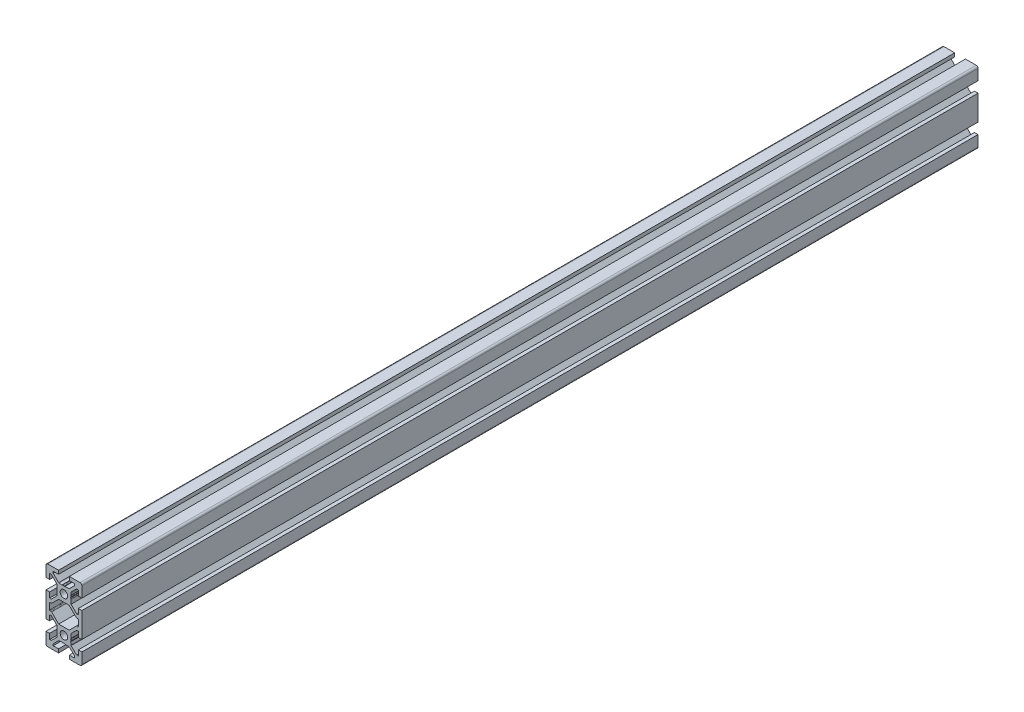
SolidWorks part; units mm, degrees
ref_plane "Front Plane" through (0, 0, 0) normal (0, 0, 1) x (1, 0, 0)
ref_plane "Top Plane" through (0, 0, 0) normal (0, 1, 0) x (1, 0, 0)
ref_plane "Right Plane" through (0, 0, 0) normal (1, 0, 0) x (0, 0, -1)
ref_plane "Plane1" through (0, 0, -600) normal (0, 0, -1) x (-1, 0, 0)
sketch "Sketch1" plane through (0, 0, -600) normal (0, 0, -1) x (-1, 0, 0)
  line L0 (8, 1.7) -> (8, -1.7)
  line L1 (7.7, -2) -> (7.0636, -2)
  line L2 (6.8515, -2.0879) -> (2.9393, -6)
  line L3 (2.9393, -6) -> (-2.9393, -6)
  line L4 (-2.9393, -6) -> (-6.8515, -2.0879)
  line L5 (-7.0636, -2) -> (-7.7, -2)
  line L6 (-8, -1.7) -> (-8, 1.7)
  line L7 (-7.7, 2) -> (-7.0636, 2)
  line L8 (-6.8515, 2.0879) -> (-2.9393, 6)
  line L9 (-2.9393, 6) -> (2.9393, 6)
  line L10 (2.9393, 6) -> (6.8515, 2.0879)
  line L11 (7.0636, 2) -> (7.7, 2)
  line L12 (10, -7) -> (10, 7)
  line L13 (10, 7) -> (8, 7)
  line L14 (8, 7) -> (8, 4)
  line L15 (8, 4) -> (7.0607, 4)
  line L16 (7.0607, 4) -> (4, 7.0607)
  line L17 (4, 7.0607) -> (4, 7.5)
  line L18 (4, 7.5) -> (3.751, 8.7811)
  line L19 (3.751, 8.7811) -> (3.933, 9.0964)
  line L20 (3.933, 9.5964) -> (3.7, 10)
  line L21 (3.7, 10) -> (3.933, 10.4036)
  line L22 (4, 10.6536) -> (4, 12.9393)
  line L23 (4, 12.9393) -> (7.0607, 16)
  line L24 (7.0607, 16) -> (8, 16)
  line L25 (8, 16) -> (8, 13)
  line L26 (8, 13) -> (10, 13)
  line L27 (10, 13) -> (10, 19)
  line L28 (9, 20) -> (3, 20)
  line L29 (3, 20) -> (3, 18)
  line L30 (3, 18) -> (6, 18)
  line L31 (6, 18) -> (6, 17.0607)
  line L32 (6, 17.0607) -> (2.9393, 14)
  line L33 (2.9393, 14) -> (2.5, 14)
  line L34 (2.5, 14) -> (1.2189, 13.751)
  line L35 (1.2189, 13.751) -> (0.9036, 13.933)
  line L36 (0.4036, 13.933) -> (0, 13.7)
  line L37 (0, 13.7) -> (-0.4036, 13.933)
  line L38 (-0.6536, 14) -> (-2.9393, 14)
  line L39 (-2.9393, 14) -> (-6, 17.0607)
  line L40 (-6, 17.0607) -> (-6, 18)
  line L41 (-6, 18) -> (-3, 18)
  line L42 (-3, 18) -> (-3, 20)
  line L43 (-3, 20) -> (-9, 20)
  line L44 (-10, 19) -> (-10, 13)
  line L45 (-10, 13) -> (-8, 13)
  line L46 (-8, 13) -> (-8, 16)
  line L47 (-8, 16) -> (-7.0607, 16)
  line L48 (-7.0607, 16) -> (-4, 12.9393)
  line L49 (-4, 12.9393) -> (-4, 12.5)
  line L50 (-4, 12.5) -> (-3.751, 11.2189)
  line L51 (-3.751, 11.2189) -> (-3.933, 10.9036)
  line L52 (-3.933, 10.4036) -> (-3.7, 10)
  line L53 (-3.7, 10) -> (-3.933, 9.5964)
  line L54 (-4, 9.3464) -> (-4, 7.0607)
  line L55 (-4, 7.0607) -> (-7.0607, 4)
  line L56 (-7.0607, 4) -> (-8, 4)
  line L57 (-8, 4) -> (-8, 7)
  line L58 (-8, 7) -> (-10, 7)
  line L59 (-10, 7) -> (-10, -7)
  line L60 (-10, -7) -> (-8, -7)
  line L61 (-8, -7) -> (-8, -4)
  line L62 (-8, -4) -> (-7.0607, -4)
  line L63 (-7.0607, -4) -> (-4, -7.0607)
  line L64 (-4, -7.0607) -> (-4, -9.3464)
  line L65 (-3.933, -9.5964) -> (-3.7, -10)
  line L66 (-3.7, -10) -> (-3.933, -10.4036)
  line L67 (-3.933, -10.9036) -> (-3.751, -11.2189)
  line L68 (-3.751, -11.2189) -> (-4, -12.5)
  line L69 (-4, -12.5) -> (-4, -12.9393)
  line L70 (-4, -12.9393) -> (-7.0607, -16)
  line L71 (-7.0607, -16) -> (-8, -16)
  line L72 (-8, -16) -> (-8, -13)
  line L73 (-8, -13) -> (-10, -13)
  line L74 (-10, -13) -> (-10, -19)
  line L75 (-9, -20) -> (-3, -20)
  line L76 (-3, -20) -> (-3, -18)
  line L77 (-3, -18) -> (-6, -18)
  line L78 (-6, -18) -> (-6, -17.0607)
  line L79 (-6, -17.0607) -> (-2.9393, -14)
  line L80 (-2.9393, -14) -> (-0.6536, -14)
  line L81 (-0.4036, -13.933) -> (0, -13.7)
  line L82 (0, -13.7) -> (0.4036, -13.933)
  line L83 (0.9036, -13.933) -> (1.2189, -13.751)
  line L84 (1.2189, -13.751) -> (2.5, -14)
  line L85 (2.5, -14) -> (2.9393, -14)
  line L86 (2.9393, -14) -> (6, -17.0607)
  line L87 (6, -17.0607) -> (6, -18)
  line L88 (6, -18) -> (3, -18)
  line L89 (3, -18) -> (3, -20)
  line L90 (3, -20) -> (9, -20)
  line L91 (10, -19) -> (10, -13)
  line L92 (10, -13) -> (8, -13)
  line L93 (8, -13) -> (8, -16)
  line L94 (8, -16) -> (7.0607, -16)
  line L95 (7.0607, -16) -> (4, -12.9393)
  line L96 (4, -12.9393) -> (4, -10.6536)
  line L97 (3.933, -10.4036) -> (3.7, -10)
  line L98 (3.7, -10) -> (3.933, -9.5964)
  line L99 (3.933, -9.0964) -> (3.751, -8.7811)
  line L100 (3.751, -8.7811) -> (4, -7.5)
  line L101 (4, -7.5) -> (4, -7.0607)
  line L102 (4, -7.0607) -> (7.0607, -4)
  line L103 (7.0607, -4) -> (8, -4)
  line L104 (8, -4) -> (8, -7)
  line L105 (8, -7) -> (10, -7)
  circle A0 centre (0, -10) radius 2.1
  circle A1 centre (0, 10) radius 2.1
  arc A2 (7.7, 2) -> (8, 1.7) centre (7.7, 1.7) cw
  arc A3 (8, -1.7) -> (7.7, -2) centre (7.7, -1.7) cw
  arc A4 (7.0636, -2) -> (6.8515, -2.0879) centre (7.0636, -2.3) ccw
  arc A5 (-6.8515, -2.0879) -> (-7.0636, -2) centre (-7.0636, -2.3) ccw
  arc A6 (-7.7, -2) -> (-8, -1.7) centre (-7.7, -1.7) cw
  arc A7 (-8, 1.7) -> (-7.7, 2) centre (-7.7, 1.7) cw
  arc A8 (-7.0636, 2) -> (-6.8515, 2.0879) centre (-7.0636, 2.3) ccw
  arc A9 (6.8515, 2.0879) -> (7.0636, 2) centre (7.0636, 2.3) ccw
  arc A10 (3.933, 9.0964) -> (3.933, 9.5964) centre (3.5, 9.3464) ccw
  arc A11 (3.933, 10.4036) -> (4, 10.6536) centre (3.5, 10.6536) ccw
  arc A12 (10, 19) -> (9, 20) centre (9, 19) ccw
  arc A13 (0.9036, 13.933) -> (0.4036, 13.933) centre (0.6536, 13.5) ccw
  arc A14 (-0.4036, 13.933) -> (-0.6536, 14) centre (-0.6536, 13.5) ccw
  arc A15 (-9, 20) -> (-10, 19) centre (-9, 19) ccw
  arc A16 (-3.933, 10.9036) -> (-3.933, 10.4036) centre (-3.5, 10.6536) ccw
  arc A17 (-3.933, 9.5964) -> (-4, 9.3464) centre (-3.5, 9.3464) ccw
  arc A18 (-4, -9.3464) -> (-3.933, -9.5964) centre (-3.5, -9.3464) ccw
  arc A19 (-3.933, -10.4036) -> (-3.933, -10.9036) centre (-3.5, -10.6536) ccw
  arc A20 (-10, -19) -> (-9, -20) centre (-9, -19) ccw
  arc A21 (-0.6536, -14) -> (-0.4036, -13.933) centre (-0.6536, -13.5) ccw
  arc A22 (0.4036, -13.933) -> (0.9036, -13.933) centre (0.6536, -13.5) ccw
  arc A23 (9, -20) -> (10, -19) centre (9, -19) ccw
  arc A24 (4, -10.6536) -> (3.933, -10.4036) centre (3.5, -10.6536) ccw
  arc A25 (3.933, -9.5964) -> (3.933, -9.0964) centre (3.5, -9.3464) ccw
  dimension "D1" = 4.2
  dimension "D3" = 0.3
  dimension "D4" = 0.3
  dimension "D5" = 0.3
  dimension "D6" = 0.3
  dimension "D7" = 0.3
  dimension "D8" = 0.3
  dimension "D9" = 0.3
  dimension "D10" = 0.5
  dimension "D11" = 0.5
  dimension "D12" = 1
  dimension "D13" = 0.5
  dimension "D14" = 0.5
  dimension "D15" = 1
  dimension "D16" = 0.5
  dimension "D17" = 0.5
  dimension "D18" = 0.5
  dimension "D19" = 0.5
  dimension "D20" = 0.4036
  dimension "D21" = 0.5
  dimension "D22" = 0.5
  dimension "D23" = 1
  dimension "D24" = 0.5
  dimension "D25" = 0.5
  dimension "D26" = 0.4036
  dimension "D27" = 0.6536
  dimension "D28" = 0.6536
  dimension "D29" = 0.9036
  dimension "D30" = 0.9036
  dimension "D31" = 1.2189
  dimension "D32" = 1.2189
  dimension "D33" = 2.5
  dimension "D34" = 2.5
  dimension "D35" = 2.9393
  dimension "D36" = 2.9393
  dimension "D37" = 3
  dimension "D38" = 3.5
  dimension "D39" = 6
  dimension "D40" = 6.8515
  dimension "D41" = 3.7
  dimension "D42" = 3.7
  dimension "D43" = 3.751
  dimension "D44" = 3.751
  dimension "D45" = 3.933
  dimension "D46" = 3.933
  dimension "D47" = 6.8515
  dimension "D48" = 7.0607
  dimension "D49" = 7.0607
  dimension "D50" = 7.0636
  dimension "D51" = 7.0636
  dimension "D52" = 8
  dimension "D53" = 10
  dimension "D54" = 3
  dimension "D55" = 4
  dimension "D56" = 6
  dimension "D57" = 6.8515
  dimension "D58" = 6.8515
  dimension "D59" = 7.0607
  dimension "D60" = 7.0607
  dimension "D61" = 0.4036
  dimension "D62" = 0.4036
  dimension "D63" = 0.6536
  dimension "D64" = 0.6536
  dimension "D65" = 2.9393
  dimension "D66" = 2.9393
  dimension "D67" = 8
  dimension "D68" = 2
  dimension "D69" = 3.5
  dimension "D70" = 3.5
  dimension "D71" = 3.7
  dimension "D72" = 3.7
  dimension "D73" = 3.751
  dimension "D74" = 3.751
  dimension "D75" = 3.933
  dimension "D76" = 3.933
  dimension "D77" = 4
  dimension "D78" = 6
  dimension "D79" = 7
  dimension "D80" = 7.0607
  dimension "D81" = 7.0607
  dimension "D82" = 7.5
  dimension "D83" = 8.7811
  dimension "D84" = 9.0964
  dimension "D85" = 9.3464
  dimension "D86" = 9.3464
  dimension "D87" = 9.5964
  dimension "D88" = 9.5964
  dimension "D89" = 10.4036
  dimension "D90" = 12.5
  dimension "D91" = 13
  dimension "D92" = 13.5
  dimension "D93" = 13.5
  dimension "D94" = 18
  dimension "D95" = 20
  dimension "D96" = 2
  dimension "D97" = 4
  dimension "D98" = 6
  dimension "D99" = 7
  dimension "D100" = 7.0607
  dimension "D101" = 7.0607
  dimension "D102" = 7.5
  dimension "D103" = 8.7811
  dimension "D104" = 9.0964
  dimension "D105" = 9.3464
  dimension "D106" = 9.3464
  dimension "D107" = 9.5964
  dimension "D108" = 9.5964
  dimension "D109" = 10.4036
  dimension "D110" = 12.5
  dimension "D111" = 13
  dimension "D112" = 18
extrude "Boss-Extrude1" add sketch "Sketch1" against normal blind 500
